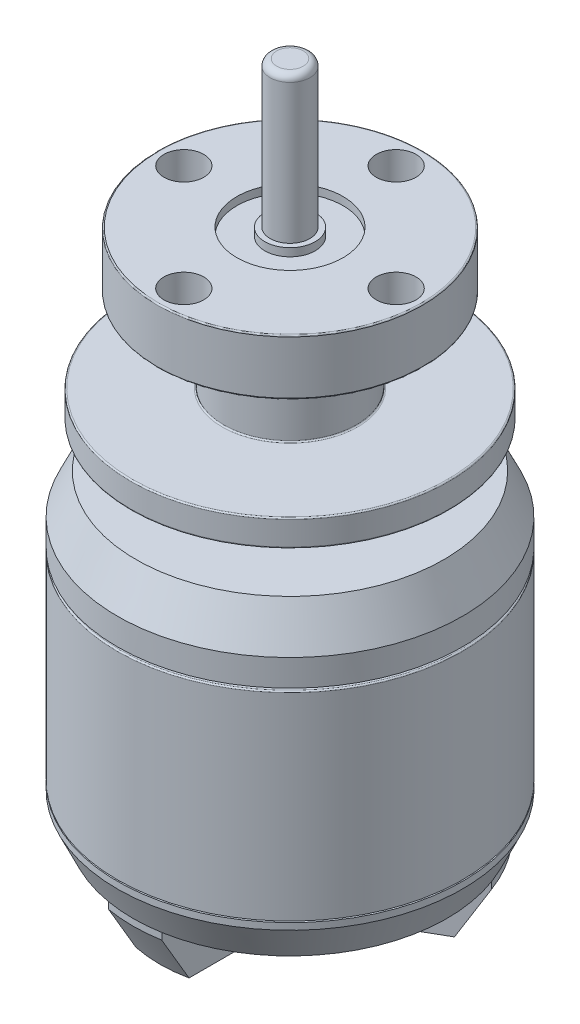
SolidWorks part; units mm, degrees
ref_plane "Front Plane" through (0, 0, 0) normal (0, 0, 1) x (1, 0, 0)
ref_plane "Top Plane" through (0, 0, 0) normal (0, 1, 0) x (1, 0, 0)
ref_plane "Right Plane" through (0, 0, 0) normal (1, 0, 0) x (0, 0, -1)
sketch "Sketch1" plane through (0, 0, 0) normal (0, 1, 0) x (1, 0, 0)
  circle A0 centre (0, 0) radius 13
  dimension "D1" = 26
extrude "Boss-Extrude1" add sketch "Sketch1" along normal blind 15
sketch "Sketch2" plane through (0, 15, 0) normal (0, 1, 0) x (1, 0, 0)
  circle A0 centre (0, 0) radius 7
extrude "Boss-Extrude2" add sketch "Sketch2" along normal blind 0.2
sketch "Sketch4" plane through (0, 15.2, 0) normal (0, 1, 0) x (1, 0, 0)
  circle A0 centre (0, 0) radius 13
extrude "Boss-Extrude3" add sketch "Sketch4" along normal blind 5
sketch "Sketch5" plane through (0, 20.2, 0) normal (0, 1, 0) x (1, 0, 0)
  circle A0 centre (0, 0) radius 5
extrude "Boss-Extrude4" add sketch "Sketch5" along normal blind 3.4
sketch "Sketch6" plane through (0, 23.6, 0) normal (0, 1, 0) x (1, 0, 0)
  circle A0 centre (0, 0) radius 12
extrude "Boss-Extrude5" add sketch "Sketch6" along normal blind 2
sketch "Sketch7" plane through (0, 25.6, 0) normal (0, 1, 0) x (1, 0, 0)
  circle A0 centre (0, 0) radius 5
extrude "Boss-Extrude6" add sketch "Sketch7" along normal blind 6.3
sketch "Sketch8" plane through (0, 31.9, 0) normal (0, 1, 0) x (1, 0, 0)
  circle A0 centre (0, 0) radius 10
extrude "Boss-Extrude7" add sketch "Sketch8" along normal blind 4.2
chamfer "Chamfer1" distance 3 angle 25 1 edges at (0, 20.2, 13)
fillet "Fillet1" radius 0.1 9 edges at (0, 31.9, 10) (0, 36.1, 10) (0, 23.6, 12) (0, 25.6, 12) (0, 15, 13) (0, 20.2, 5) (0, 23.6, 5) (0, 25.6, 5) (0, 31.9, 5)
sketch "Sketch9" plane through (0, 0, 0) normal (0, -1, 0) x (1, 0, 0)
  circle A0 centre (0, 0) radius 8.4636
extrude "Boss-Extrude8" add sketch "Sketch9" along normal blind 0.1
sketch "Sketch10" plane through (0, -0.1, 0) normal (0, -1, 0) x (1, 0, 0)
  circle A0 centre (0, 0) radius 13
extrude "Boss-Extrude9" add sketch "Sketch10" along normal blind 3
chamfer "Chamfer2" distance 2.5 angle 25 1 edges at (0, -3.1, -13)
sketch "Sketch12" plane through (0, -3.1, 0) normal (0, -1, 0) x (1, 0, 0)
  line L0 (0, 11.8342) -> (0, 0) construction
  line L1 (0, 0) -> (10.2487, -5.9171) construction
  line L2 (0, 0) -> (-10.2487, -5.9171) construction
  line L3 (-11.2487, -4.1851) -> (-1, 1.7321)
  line L4 (-11.2487, -4.1851) -> (-9.2487, -7.6492)
  line L5 (-1, 1.7321) -> (1, -1.7321)
  line L6 (-9.2487, -7.6492) -> (1, -1.7321)
  line L7 (-11.2487, -4.1851) -> (1, -1.7321) construction
  line L8 (-1, 1.7321) -> (-9.2487, -7.6492) construction
  line L9 (-2, 0) -> (-2, 11.8342)
  line L10 (-2, 0) -> (2, 0)
  line L11 (-2, 11.8342) -> (2, 11.8342)
  line L12 (2, 0) -> (2, 11.8342)
  line L13 (-2, 0) -> (2, 11.8342) construction
  line L14 (-2, 11.8342) -> (2, 0) construction
  line L15 (1, 1.7321) -> (11.2487, -4.1851)
  line L16 (1, 1.7321) -> (-1, -1.7321)
  line L17 (11.2487, -4.1851) -> (9.2487, -7.6492)
  line L18 (-1, -1.7321) -> (9.2487, -7.6492)
  line L19 (1, 1.7321) -> (9.2487, -7.6492) construction
  line L20 (11.2487, -4.1851) -> (-1, -1.7321) construction
  circle A0 centre (0, 0) radius 5
  circle A1 centre (0, 0) radius 11.8342 construction
  circle A2 centre (0, 0) radius 11.8342
  point P9 (-5.1244, -2.9586)
  point P10 (0, 5.9171)
  point P15 (5.1244, -2.9586)
  circle M10 centre (0, 0) radius 11.8342
extrude "Boss-Extrude10" add sketch "Sketch12" along normal blind 4 contours A0 L3 L6 M10 | L3 A0 L6 L18 L16 L10 L9 | L6 A0 L18 | L18 A0 L15 L12 L10 L5 L6 | A0 L18 L15 M10 | L16 L18 L6 L5 | L15 L16 L10 L12 | L15 A0 L12 | L12 A0 L9 L3 L5 L16 L15 | L9 A0 L3 | A0 L12 L9 M10 | L9 L10 L5 L3
chamfer "Chamfer3" distance 3.5 angle 30 3 edges at (0, -7.1, 11.8342) (10.2487, -7.1, -5.9171) (-10.2487, -7.1, -5.9171)
sketch "Sketch13" plane through (0, -3.1, 0) normal (0, -1, 0) x (1, 0, 0)
  circle A0 centre (0, 0) radius 10.7706
extrude "Cut-Extrude1" cut sketch "Sketch13" against normal blind 4
sketch "Sketch14" plane through (0, -7.1, 0) normal (0, -1, 0) x (1, 0, 0)
  circle A0 centre (0, 0) radius 4.5
extrude "Boss-Extrude11" add sketch "Sketch14" along normal blind 1
fillet "Fillet2" radius 0.7 1 edges at (0, -8.1, -4.5)
fillet "Fillet3" radius 2 6 edges at (-2, -5.1, 4.5826) (-4.9686, -5.1, -0.5592) (2, -5.1, 4.5826) (4.9686, -5.1, -0.5592) (2.9686, -5.1, -4.0233) (-2.9686, -5.1, -4.0233)
sketch "Sketch15" plane through (0, -7.1, 0) normal (0, -1, 0) x (1, 0, 0)
  circle A0 centre (0, 6.5) radius 1.5
  dimension "D1" = 6.5
  dimension "D2" = 3
extrude "Cut-Extrude2" cut sketch "Sketch15" against normal blind 4
pattern_circular "CirPattern1" count 3 over 360 about axis through (0, 0, 0) along (0, 1, 0) of "Cut-Extrude2"
sketch "Sketch16" plane through (0, -8.1, 0) normal (0, -1, 0) x (1, 0, 0)
  circle A0 centre (0, 0) radius 1.5
  circle A1 centre (0, 0) radius 1.7
extrude "Cut-Extrude3" cut sketch "Sketch16" against normal blind 2
fillet "Fillet4" radius 0.3 1 edges at (0, -8.1, -1.5)
sketch "Sketch17" plane through (0, 36.1, 0) normal (0, 1, 0) x (1, 0, 0)
  circle A0 centre (0, 0) radius 4
  circle A1 centre (0, 0) radius 1.9
extrude "Cut-Extrude4" cut sketch "Sketch17" against normal blind 0.6
sketch "Sketch18" plane through (0, 36.1, 0) normal (0, 1, 0) x (1, 0, 0)
  circle A1 centre (0, 0) radius 1.5
extrude "Boss-Extrude12" add sketch "Sketch18" along normal blind 11
fillet "Fillet5" radius 0.5 1 edges at (0, 47.1, 1.5)
sketch "Sketch19" plane through (0, 36.1, 0) normal (0, 1, 0) x (1, 0, 0)
  circle A0 centre (0, 8) radius 1.5
  dimension "D1" = 3
  dimension "D2" = 8
extrude "Cut-Extrude5" cut sketch "Sketch19" against normal blind 5
pattern_circular "CirPattern2" count 4 over 360 about axis through (0, 0, 0) along (0, 1, 0) of "Cut-Extrude5"
